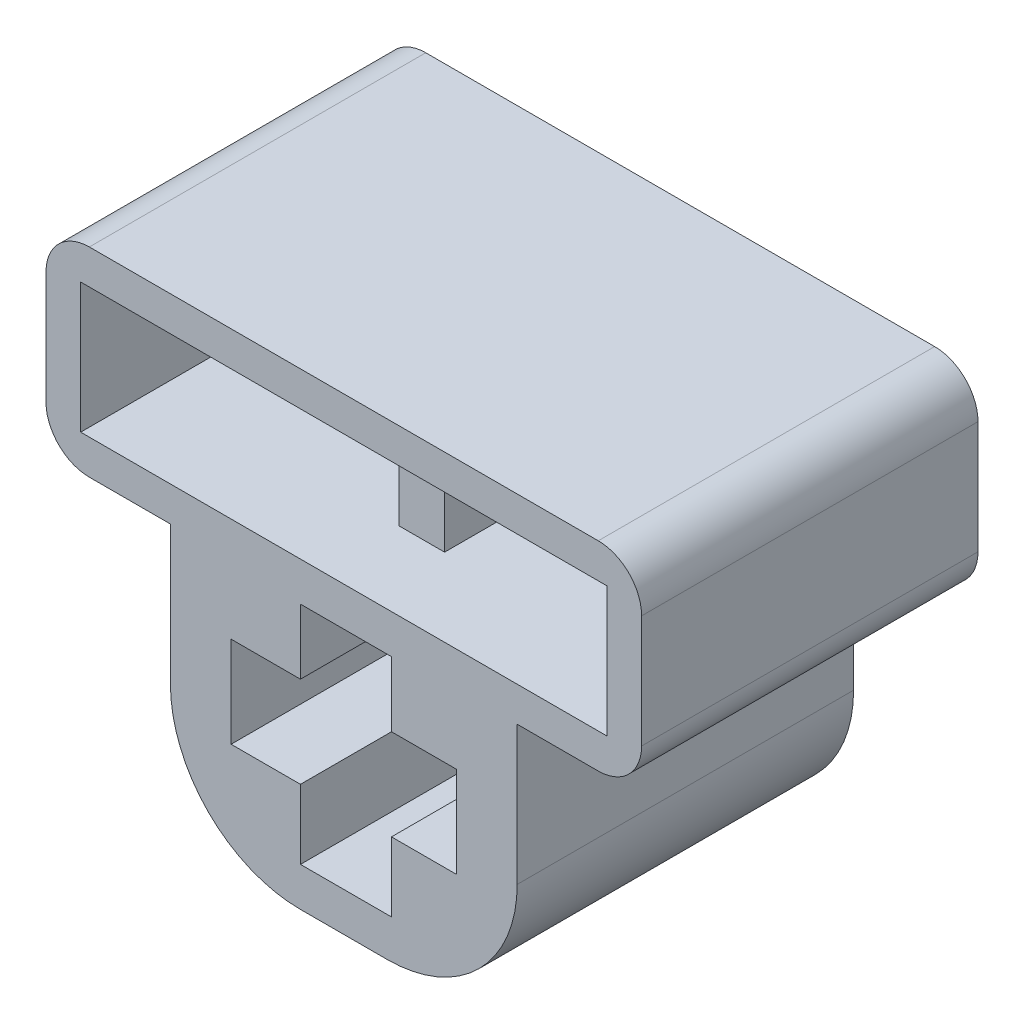
SolidWorks part; units mm, degrees
ref_plane "Front Plane" through (0, 0, 0) normal (0, 0, 1) x (1, 0, 0)
ref_plane "Top Plane" through (0, 0, 0) normal (0, 1, 0) x (1, 0, 0)
ref_plane "Right Plane" through (0, 0, 0) normal (1, 0, 0) x (0, 0, -1)
sketch "Sketch1" plane through (0, 0, 0) normal (0, 0, 1) x (1, 0, 0)
  line L5 (-4, 3.5) -> (4, 3.5)
  line L6 (-4, 3.5) -> (-4, -3.5)
  line L7 (-4, -3.5) -> (4, -3.5)
  line L8 (4, 3.5) -> (4, -3.5)
  line L9 (-4, 3.5) -> (4, -3.5) construction
  line L10 (-4, -3.5) -> (4, 3.5) construction
  point P0 (0, 0)
  dimension "D1" = 7
  dimension "D4" = 8
extrude "Boss-Extrude1" add sketch "Sketch1" along normal blind 7.76
sketch "Sketch6" plane through (0, 0, 7.76) normal (0, 0, 1) x (1, 0, 0)
  line L0 (1.1, -1) -> (2.6, -1)
  line L5 (-2.6, 1.1) -> (-1, 1.1)
  line L6 (-2.6, 1.1) -> (-2.6, -1)
  line L7 (-2.6, -1) -> (-1, -1)
  line L8 (2.6, 1.1) -> (2.6, -1)
  line L9 (1.1, 1.1) -> (2.6, 1.1)
  line L11 (-1, 2.6) -> (1.1, 2.6)
  line L12 (-1, 2.6) -> (-1, 1.1)
  line L13 (-1, -2.6) -> (1.1, -2.6)
  line L14 (1.1, 2.6) -> (1.1, 1.1)
  line L15 (-4, 3.5) -> (-4, -3.5) construction
  line L16 (1.1, -1) -> (1.1, -2.6)
  line L17 (-1.2905, 1.1) -> (-1, 1.2845) construction
  line L19 (-1, -1) -> (-1, -2.6)
  line L20 (-4, -3.5) -> (4, -3.5) construction
  point P0 (0, 0)
  point P6 (-1.6425, -0.6151)
  point P21 (-4, 0)
  dimension "D1" = 5.2
  dimension "D2" = 2.1
  dimension "D3" = 5.2
  dimension "D4" = 2.1
  dimension "D5" = 1.6
  dimension "D6" = 1.6
  dimension "D7" = 1.4
  dimension "D8" = 0.9
extrude "Cut-Extrude3" cut sketch "Sketch6" against normal through all
sketch "Sketch7" plane through (-4, 0, 0) normal (-1, 0, 0) x (0, 0, 1)
  line L0 (7.76, 3.5) -> (7.76, -3.5) construction
  line L1 (0, 3.5) -> (7.76, 3.5)
  line L2 (0, 3.5) -> (0, 2.7)
  line L3 (0, 2.7) -> (7.76, 2.7)
  line L4 (7.76, 3.5) -> (7.76, 2.7)
  dimension "D1" = 0.8
extrude "Boss-Extrude2" add sketch "Sketch7" along normal blind 2.87
sketch "Sketch9" plane through (4, 0, 0) normal (1, 0, 0) x (0, 0, -1)
  line L5 (0, 3.5) -> (0, -3.5) construction
  line L6 (-7.76, 3.5) -> (0, 3.5)
  line L7 (-7.76, 3.5) -> (-7.76, 2.7)
  line L8 (-7.76, 2.7) -> (0, 2.7)
  line L9 (0, 3.5) -> (0, 2.7)
  dimension "D1" = 0.8
extrude "Boss-Extrude3" add sketch "Sketch9" along normal blind 2.87
sketch "Sketch10" plane through (0, 3.5, 0) normal (0, 1, 0) x (1, 0, 0)
  line L0 (-6.87, 0) -> (6.87, 0) construction
  line L1 (6.87, -7.76) -> (6.07, -7.76)
  line L2 (6.87, -7.76) -> (6.87, 0)
  line L3 (6.87, 0) -> (6.07, 0)
  line L4 (6.07, -7.76) -> (6.07, 0)
  dimension "D1" = 0.8
extrude "Boss-Extrude4" add sketch "Sketch10" along normal blind 3
sketch "Sketch11" plane through (0, 3.5, 0) normal (0, 1, 0) x (1, 0, 0)
  line L0 (-6.87, 0) -> (6.07, 0) construction
  line L1 (-6.87, -7.76) -> (-6.07, -7.76)
  line L2 (-6.87, -7.76) -> (-6.87, 0)
  line L3 (-6.87, 0) -> (-6.07, 0)
  line L4 (-6.07, -7.76) -> (-6.07, 0)
  dimension "D1" = 0.8
extrude "Boss-Extrude5" add sketch "Sketch11" along normal blind 3
sketch "Sketch12" plane through (0, 6.5, 0) normal (0, 1, 0) x (1, 0, 0)
  line L1 (6.87, -7.76) -> (-6.87, -7.76)
  line L2 (6.87, -7.76) -> (6.87, 0)
  line L3 (6.87, 0) -> (-6.87, 0)
  line L4 (-6.87, -7.76) -> (-6.87, 0)
extrude "Boss-Extrude6" add sketch "Sketch12" along normal blind 0.8
sketch "Sketch14" plane through (0, 3.5, 0) normal (0, 1, 0) x (1, 0, 0)
  line L0 (-6.07, -7.76) -> (6.07, -7.76) construction
  line L1 (0.525, -0.0038) -> (-0.525, -0.0038)
  line L2 (0.525, -0.0038) -> (0.525, -5.96)
  line L3 (0.525, -5.96) -> (-0.525, -5.96)
  line L4 (-0.525, -0.0038) -> (-0.525, -5.96)
  dimension "D1" = 5.545
  dimension "D2" = 1.05
  dimension "D3" = 1.05
  dimension "D4" = 1.8
extrude "Boss-Extrude7" add sketch "Sketch14" along normal through all
fillet "Fillet4" radius 1 1 edges at (-6.87, 7.3, 3.88)
fillet "Fillet5" radius 1 1 edges at (6.87, 7.3, 3.88)
fillet "Fillet6" radius 1 1 edges at (-6.87, 2.7, 3.88)
fillet "Fillet7" radius 1 1 edges at (6.87, 2.7, 3.88)
fillet "Fillet8" radius 3 1 edges at (4, -3.5, 3.88)
fillet "Fillet9" radius 3 1 edges at (-4, -3.5, 3.88)
